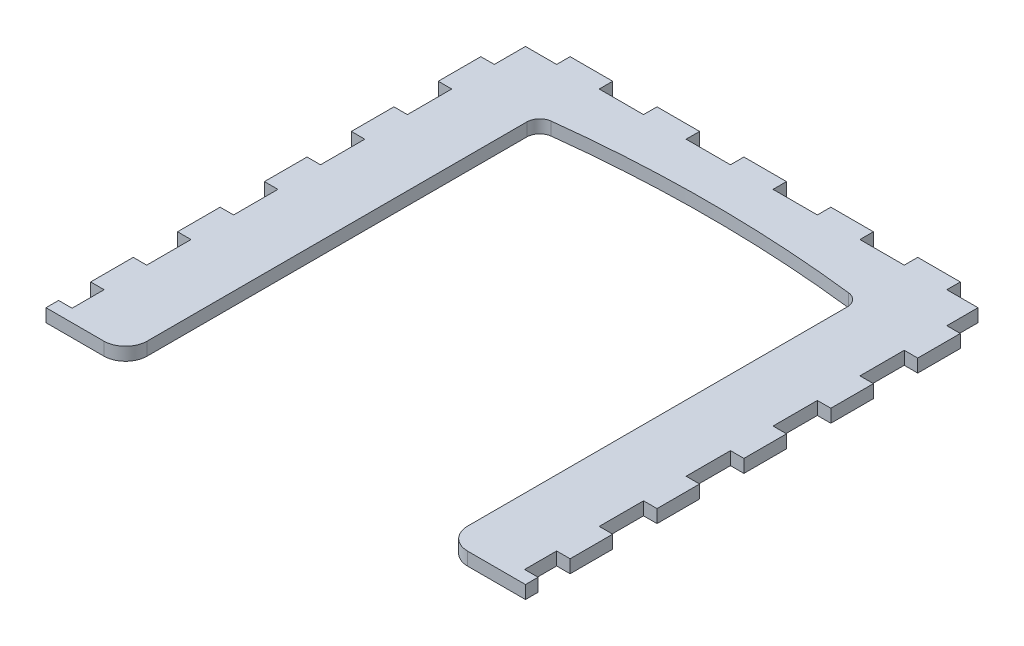
SolidWorks part; units mm, degrees
ref_plane "Front Plane" through (0, 0, 0) normal (0, 0, 1) x (1, 0, 0)
ref_plane "Top Plane" through (0, 0, 0) normal (0, 1, 0) x (1, 0, 0)
ref_plane "Right Plane" through (0, 0, 0) normal (1, 0, 0) x (0, 0, -1)
sketch "Sketch1" plane through (0, 0, 0) normal (0, 1, 0) x (1, 0, 0)
  line L0 (0, 0) -> (0, 21) construction
  line L5 (55.1722, -43.5014) -> (55.1722, 66.843)
  line L6 (55.1722, 66.843) -> (36.8722, 66.843)
  line L7 (36.8722, 66.843) -> (36.8722, -43.5014)
  line L8 (36.8722, -43.5014) -> (55.1722, -43.5014)
  line L9 (55.1722, -43.5014) -> (55.1722, 66.843)
  line L10 (55.1722, 66.843) -> (36.8722, 66.843) construction
  line L11 (36.8722, 66.843) -> (36.8722, -43.5014) construction
  line L12 (41.8722, -43.5014) -> (55.1722, -43.5014)
  line L13 (-55.1722, 66.843) -> (-55.1722, -43.5014)
  line L14 (-55.1722, -43.5014) -> (-36.8722, -43.5014)
  line L15 (-36.8722, -43.5014) -> (-36.8722, 66.843)
  line L16 (-36.8722, 66.843) -> (-55.1722, 66.843)
  line L17 (-55.1722, 66.843) -> (-55.1722, -43.5014)
  line L18 (-55.1722, -43.5014) -> (-41.8722, -43.5014)
  line L19 (-36.8722, -43.5014) -> (-36.8722, 66.843) construction
  line L20 (-36.8722, 66.843) -> (-55.1722, 66.843) construction
  line L37 (-55.1722, 66.843) -> (55.1722, 66.843)
  line L38 (-55.1722, 48.843) -> (55.1722, 48.843) construction
  line L39 (0, 63.843) -> (0, 48.843) construction
  line L40 (0, -84.9014) -> (0, -99.9014) construction
  line L41 (51.8722, -99.9014) -> (-51.8722, -99.9014) construction
  line L42 (51.8722, -84.9014) -> (-51.8722, -84.9014) construction
  line L43 (52.1722, 63.843) -> (-52.1722, 63.843) construction
  line L44 (-36.8722, 53.843) -> (36.8722, 53.843) construction
  line L45 (-36.8722, 48.843) -> (-36.8722, -38.5014)
  line L46 (36.8722, 48.843) -> (36.8722, -38.5014)
  circle A0 centre (0, 0) radius 21 construction
  circle A1 centre (0, 0) radius 21 construction
  arc A2 (-34.2253, 51.8221) -> (-36.8722, 48.843) centre (-33.8722, 48.843) ccw
  arc A3 (-34.2253, 51.8221) -> (34.2253, 51.8221) centre (0, -236.9888) cw
  arc A4 (34.2253, 51.8221) -> (36.8722, 48.843) centre (33.8722, 48.843) cw
  arc A5 (41.8722, -43.5014) -> (36.8722, -38.5014) centre (41.8722, -38.5014) cw
  arc A6 (-41.8722, -43.5014) -> (-36.8722, -38.5014) centre (-41.8722, -38.5014) ccw
  dimension "D3" = 3
  dimension "D5" = 5
  dimension "D4" = 13
  dimension "D1" = 0
  dimension "D2" = 0
extrude "Boss-Extrude1" add sketch "Sketch1" along normal up to vertex (3 mm away)
sketch "Sketch2" plane through (0, 0, 0) normal (0, 1, 0) x (1, 0, 0)
  line L0 (-55.2722, -40.5014) -> (-52.0722, -40.5014) construction
  line L1 (-55.2722, -40.6014) -> (-52.0722, -40.6014)
  line L2 (-52.0722, -40.6014) -> (-52.0722, -33.2292)
  line L3 (-55.2722, -40.6014) -> (-55.2722, -33.2292)
  line L4 (-52.0722, 6.7708) -> (-55.2722, 6.7708)
  line L5 (-55.2722, 6.7708) -> (-55.2722, -3.4292)
  line L6 (-46.7722, 63.743) -> (-46.7722, 66.943)
  line L7 (-46.7722, 66.943) -> (-55.2722, 66.943)
  line L8 (-55.2722, 66.943) -> (-55.2722, 56.5708)
  line L9 (-55.2722, 56.5708) -> (-52.0722, 56.5708)
  line L10 (-52.0722, 56.5708) -> (-52.0722, 63.743)
  line L11 (-52.0722, 63.743) -> (-46.7722, 63.743)
  line L12 (-44.9, 63.743) -> (-44.9, 66.943)
  line L13 (-44.9, 66.943) -> (-55.2722, 66.943)
  line L14 (-55.2722, 66.943) -> (-55.2722, 56.5708)
  line L15 (-55.2722, 56.5708) -> (-52.0722, 56.5708)
  line L16 (-52.0722, 56.5708) -> (-52.0722, 63.743)
  line L17 (-52.0722, 63.743) -> (-44.9, 63.743)
  line L18 (-46.7722, -40.4014) -> (-52.0722, -40.4014)
  line L19 (-46.7722, -43.6014) -> (-46.7722, -40.4014)
  line L20 (-55.2722, -43.6014) -> (-46.7722, -43.6014)
  line L21 (-55.2722, -33.2292) -> (-55.2722, -43.6014)
  line L22 (-52.0722, -33.2292) -> (-55.2722, -33.2292)
  line L23 (-52.0722, -40.4014) -> (-52.0722, -33.2292)
  line L24 (-46.7722, -40.4014) -> (-52.0722, -40.4014) construction
  line L25 (-46.7722, -43.6014) -> (-46.7722, -40.4014) construction
  line L26 (-55.2722, -43.6014) -> (-46.7722, -43.6014) construction
  line L27 (-55.2722, -33.2292) -> (-55.2722, -43.6014) construction
  line L28 (-52.0722, -33.2292) -> (-55.2722, -33.2292)
  line L29 (-52.0722, -40.4014) -> (-52.0722, -33.2292) construction
  line L30 (-55.2722, -3.4292) -> (-52.0722, -3.4292)
  line L31 (-52.0722, -3.4292) -> (-52.0722, 6.7708)
  line L32 (-52.0722, 6.7708) -> (-55.2722, 6.7708)
  line L33 (-55.2722, 6.7708) -> (-55.2722, -3.4292)
  line L34 (-55.2722, -3.4292) -> (-52.0722, -3.4292)
  line L35 (-52.0722, -3.4292) -> (-52.0722, 6.7708)
  line L36 (-52.0722, -13.2292) -> (-55.2722, -13.2292)
  line L37 (-52.0722, -23.4292) -> (-52.0722, -13.2292)
  line L38 (-55.2722, -23.4292) -> (-52.0722, -23.4292)
  line L39 (-55.2722, -13.2292) -> (-55.2722, -23.4292)
  line L40 (-52.0722, -13.2292) -> (-55.2722, -13.2292)
  line L41 (-52.0722, -23.4292) -> (-52.0722, -13.2292)
  line L42 (-55.2722, -23.4292) -> (-52.0722, -23.4292)
  line L43 (-55.2722, -13.2292) -> (-55.2722, -23.4292)
  line L44 (-55.2722, 16.5708) -> (-52.0722, 16.5708)
  line L45 (-55.2722, 26.7708) -> (-55.2722, 16.5708)
  line L46 (-52.0722, 26.7708) -> (-55.2722, 26.7708)
  line L47 (-52.0722, 16.5708) -> (-52.0722, 26.7708)
  line L48 (-55.2722, 16.5708) -> (-52.0722, 16.5708)
  line L49 (-55.2722, 26.7708) -> (-55.2722, 16.5708)
  line L50 (-52.0722, 26.7708) -> (-55.2722, 26.7708)
  line L51 (-52.0722, 16.5708) -> (-52.0722, 26.7708)
  line L52 (-52.0722, 46.7708) -> (-55.2722, 46.7708)
  line L53 (-55.2722, 46.7708) -> (-55.2722, 36.5708)
  line L54 (-55.2722, 36.5708) -> (-52.0722, 36.5708)
  line L55 (-52.0722, 36.5708) -> (-52.0722, 46.7708)
  line L56 (-52.0722, 46.7708) -> (-55.2722, 46.7708)
  line L57 (-55.2722, 46.7708) -> (-55.2722, 36.5708)
  line L58 (-55.2722, 36.5708) -> (-52.0722, 36.5708)
  line L59 (-52.0722, 36.5708) -> (-52.0722, 46.7708)
  line L60 (-53.6722, -40.5014) -> (-53.6722, -40.6014) construction
  line L61 (-46.9722, -42.0014) -> (-46.8722, -42.0014) construction
  line L62 (35, 65.343) -> (35.1, 65.343) construction
  line L63 (0, 0) -> (0, -43.6014) construction
  line L64 (25, 65.343) -> (24.9, 65.343) construction
  line L65 (-35.1, 63.743) -> (-35.1, 66.943)
  line L66 (-35.1, 66.943) -> (-24.9, 66.943)
  line L67 (-24.9, 63.743) -> (-24.9, 66.943)
  line L68 (-35.1, 63.743) -> (-24.9, 63.743)
  line L69 (-15.1, 63.743) -> (-15.1, 66.943)
  line L70 (-15.1, 66.943) -> (-4.9, 66.943)
  line L71 (-4.9, 63.743) -> (-4.9, 66.943)
  line L72 (-15.1, 63.743) -> (-4.9, 63.743)
  line L73 (55.2722, 36.5708) -> (52.0722, 36.5708)
  line L74 (55.2722, 46.7708) -> (55.2722, 36.5708)
  line L75 (52.0722, 46.7708) -> (55.2722, 46.7708)
  line L76 (52.0722, 36.5708) -> (52.0722, 46.7708)
  line L77 (55.2722, 16.5708) -> (52.0722, 16.5708)
  line L78 (55.2722, 26.7708) -> (55.2722, 16.5708)
  line L79 (52.0722, 26.7708) -> (55.2722, 26.7708)
  line L80 (52.0722, 16.5708) -> (52.0722, 26.7708)
  line L81 (55.2722, -3.4292) -> (52.0722, -3.4292)
  line L82 (55.2722, 6.7708) -> (55.2722, -3.4292)
  line L83 (52.0722, 6.7708) -> (55.2722, 6.7708)
  line L84 (52.0722, -3.4292) -> (52.0722, 6.7708)
  line L85 (55.2722, -23.4292) -> (52.0722, -23.4292)
  line L86 (55.2722, -13.2292) -> (55.2722, -23.4292)
  line L87 (52.0722, -13.2292) -> (55.2722, -13.2292)
  line L88 (52.0722, -23.4292) -> (52.0722, -13.2292)
  line L89 (55.2722, -40.6014) -> (52.0722, -40.6014)
  line L90 (55.2722, -40.6014) -> (55.2722, -33.2292)
  line L91 (52.0722, -33.2292) -> (55.2722, -33.2292)
  line L92 (52.0722, -40.6014) -> (52.0722, -33.2292)
  line L104 (35.1, 63.743) -> (24.9, 63.743)
  line L105 (35.1, 63.743) -> (35.1, 66.943)
  line L106 (35.1, 66.943) -> (24.9, 66.943)
  line L107 (24.9, 63.743) -> (24.9, 66.943)
  line L108 (15.1, 63.743) -> (4.9, 63.743)
  line L109 (15.1, 63.743) -> (15.1, 66.943)
  line L110 (15.1, 66.943) -> (4.9, 66.943)
  line L111 (4.9, 63.743) -> (4.9, 66.943)
  line L112 (44.9, 66.943) -> (55.2722, 66.943)
  line L113 (44.9, 63.743) -> (44.9, 66.943)
  line L114 (52.0722, 63.743) -> (44.9, 63.743)
  line L115 (52.0722, 56.5708) -> (52.0722, 63.743)
  line L116 (55.2722, 56.5708) -> (52.0722, 56.5708)
  line L117 (55.2722, 66.943) -> (55.2722, 56.5708)
  line L118 (45, 63.743) -> (45, 66.943) construction
  line L119 (45, 65.343) -> (44.9, 65.343) construction
  line L120 (46.9722, 66.843) -> (46.8722, 66.843) construction
  line L121 (35, 63.743) -> (35, 66.943) construction
  line L122 (25, 63.743) -> (25, 66.943) construction
  line L123 (15, 63.743) -> (15, 66.943) construction
  line L124 (5, 63.743) -> (5, 66.943) construction
  line L125 (15, 65.343) -> (15.1, 65.343) construction
  line L126 (5, 65.343) -> (4.9, 65.343) construction
  dimension "D1" = 0
  dimension "D2" = 0
  dimension "D3" = 0
  dimension "D4" = 0
  dimension "D5" = 0
  dimension "D6" = 0
extrude "Cut-Extrude1" cut sketch "Sketch2" along normal through all
